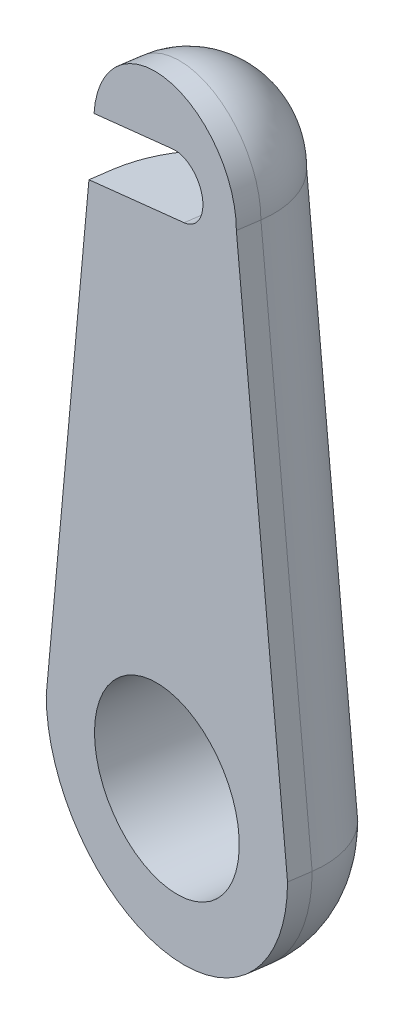
SolidWorks part; units mm, degrees
ref_plane "Front Plane" through (0, 0, 0) normal (0, 0, 1) x (1, 0, 0)
ref_plane "Top Plane" through (0, 0, 0) normal (0, 1, 0) x (1, 0, 0)
ref_plane "Right Plane" through (0, 0, 0) normal (1, 0, 0) x (0, 0, -1)
sketch "Sketch1" plane through (8.1146, -3.2834, -55.6766) normal (0.1442, 0, -0.9895) x (-0.9895, 0, -0.1442)
  line L0 (7.7839, 205.4844) -> (7.7839, 234.9484) construction
  line L1 (13.4843, 234.9484) -> (1.3539, 234.9484) construction
  line L2 (7.9153, 238.4844) -> (-3.6461, 238.4844) construction
  line L3 (-1.1061, 205.4844) -> (2.6653, 238.4844)
  line L4 (13.1653, 238.4844) -> (16.6739, 205.4844)
  line L6 (-3.6461, 244.4784) -> (-3.6461, 234.9484) construction
  line L8 (7.7839, 234.9484) -> (7.7839, 205.4844) construction
  line L9 (7.7839, 205.4844) -> (-3.6461, 205.4844) construction
  line L12 (7.7839, 205.4844) -> (7.7839, 234.9484) construction
  arc A1 (13.1653, 238.4844) -> (2.6653, 238.4844) centre (7.9153, 238.4844) ccw
  arc A2 (-1.1061, 205.4844) -> (16.6739, 205.4844) centre (7.7839, 205.4844) ccw
  dimension "D3" = 10.5
  dimension "D5" = 8.89
  dimension "D1" = 29.464
  dimension "D2" = 29.464
  dimension "D4" = 33
  dimension "D7" = 29.464
  dimension "D8" = 11.43
extrude "Base Extrude" add sketch "Sketch1" along normal blind 6.35
sketch "Sketch3" plane through (9.0304, -3.2834, -61.9602) normal (0.1442, 0, -0.9895) x (-0.9895, 0, -0.1442)
  line L0 (14.7164, 236.6382) -> (6.9306, 238.4771) construction
  line L1 (14.3026, 234.8864) -> (6.5168, 236.7253)
  line L2 (15.1301, 238.39) -> (7.3444, 240.2289)
  line L3 (6.8573, 236.9701) -> (6.8573, 237.9784) construction
  arc A0 (14.3026, 234.8864) -> (15.1301, 238.39) centre (14.7164, 236.6382) ccw
  arc A1 (7.3444, 240.2289) -> (6.5168, 236.7253) centre (6.9306, 238.4771) ccw
  circle A2 centre (6.8573, 238.4941) radius 1.524 construction
  point P3 (10.8235, 237.5577)
  dimension "D1" = 1.8
  dimension "D2" = 8
ref_plane "Rear Mirror Plane " through (-103.2134, 0, -15.0429) normal (0.9895, 0, 0.1442) x (0.1442, 0, -0.9895)
fillet "Fillet1" radius 5 4 edges at (1.1978, 240.451, -63.1018) (1.3279, 193.311, -63.0828) (-5.7332, 218.701, -64.112) (8.259, 218.701, -62.0727)
extrude "Cut-Extrude1" cut sketch "Sketch3" against normal up to surface (6.35 mm away)
mirror "Mirror2" about plane through (-103.2134, 0, -15.0429) normal (0.9895, 0, 0.1442) of bodies 109
sketch "Sketch4" plane through (9.0304, 0, -61.9602) normal (0.1442, 0, -0.9895) x (-0.9895, 0, -0.1442)
  line L0 (2.7459, 202.201) -> (7.7839, 202.201) construction
  circle A0 centre (7.7839, 202.201) radius 5.0381 construction
  circle A1 centre (7.7839, 202.201) radius 5.334
  dimension "D1" = 10.668
extrude "Cut-Extrude2" cut sketch "Sketch4" against normal up to surface (6.35 mm away) up to face at (0.0791, 224.8477, -56.8478)
mirror "Mirror3" about plane through (-103.2134, 0, -15.0429) normal (0.9895, 0, 0.1442) of "Cut-Extrude2"
delete or keep bodies "Body-Delete/Keep 1" type delete bodies bodies 112
